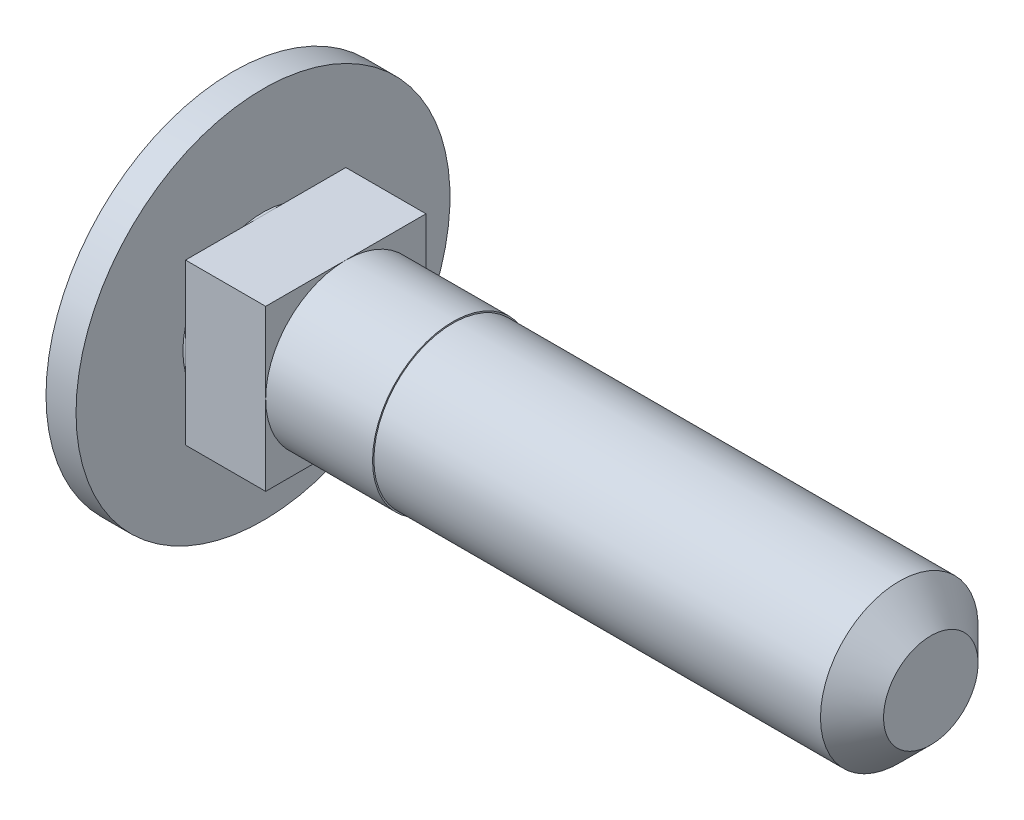
SolidWorks part; units mm, degrees
material "Серое литое железо"
ref_plane "Спереди" through (0, 0, 0) normal (0, 0, 1) x (1, 0, 0)
ref_plane "Сверху" through (0, 0, 0) normal (0, 1, 0) x (1, 0, 0)
ref_plane "Справа" through (0, 0, 0) normal (1, 0, 0) x (0, 0, -1)
sketch "Эскиз1" plane through (0, 0, 0) normal (0, 0, 1) x (1, 0, 0)
  line L0 (-121.4305, 0) -> (5950.0947, 0) construction
  line L1 (25, 0) -> (25, 2.95)
  line L2 (25, 2.95) -> (7.1, 2.95)
  line L3 (7.1, 2.95) -> (7.1, 3)
  line L4 (7.1, 3) -> (0, 3)
  line L5 (0, 3) -> (0, 7)
  line L6 (0, 7) -> (-1.1244, 7)
  line L7 (25, 0) -> (-3, 0)
  line L8 (14.4036, 16.2123) -> (32.4036, 16.2123) construction
  arc A0 (-1.1244, 7) -> (-3, 0) centre (11, 0) ccw
  point P13 (25, 1.475)
  dimension "R" = 14
  dimension "d" = 6
  dimension "D1" = 5.9
  dimension "d_D" = 14
  dimension "k" = 3
  dimension "bbb" = 17.9
  dimension "l" = 25
  dimension "b" = 18
revolve "Повернуть1" add sketch "Эскиз1" angle 360 about L0
sketch "Эскиз2" plane through (0, 0, 0) normal (1, 0, 0) x (0, 0, -1)
  line L1 (-3, 3) -> (3, 3)
  line L2 (-3, 3) -> (-3, -3)
  line L3 (-3, -3) -> (3, -3)
  line L4 (3, 3) -> (3, -3)
  line L5 (-3, 3) -> (3, -3) construction
  line L6 (-3, -3) -> (3, 3) construction
  circle A0 centre (0, 0) radius 3 construction
  circle A1 centre (0, 0) radius 3 construction
  circle A2 centre (0, 0) radius 3 construction
  point P0 (0, 0)
extrude "Бобышка-Вытянуть1" add sketch "Эскиз2" along normal blind 3 from offset 0.1
chamfer "Фаска1" distance 1.18 1 edges at (25, 0, 2.95)
equation "\"D1@Эскиз1\"=\"d@Эскиз1\"-0.1"
equation "\"D1@Фаска1\"= \"D1@Эскиз1\" / 5"
equation "\"bbb@Эскиз1\"=\"b@Эскиз1\"-0.1"
